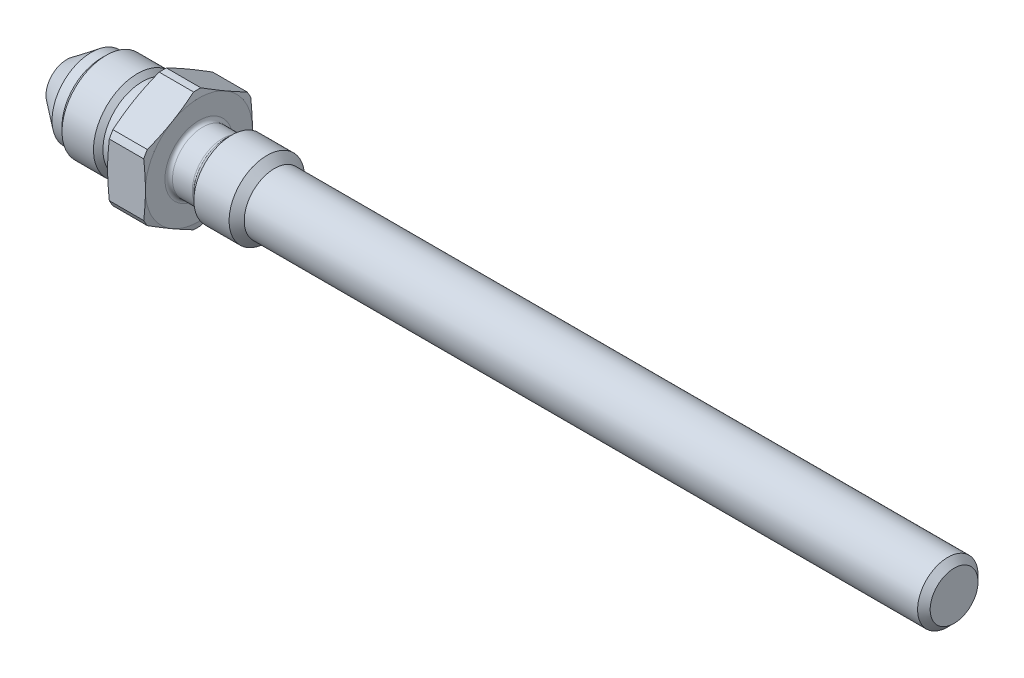
SolidWorks part; units mm, degrees
material "Сплав 3М ОСТ 1.92077-91"
ref_plane "Plane1" through (0, 0, 0) normal (0, 0, 1) x (1, 0, 0)
ref_plane "Plane2" through (0, 0, 0) normal (0, 1, 0) x (1, 0, 0)
ref_plane "Plane3" through (0, 0, 0) normal (1, 0, 0) x (0, 0, -1)
sketch "Эскиз1" plane through (0, 0, 0) normal (0, 0, 1) x (1, 0, 0)
  line L0 (0, 0) -> (-21.5, 0) construction
  line L1 (0, 8.5) -> (0, 4.8)
  line L2 (0, 4.8) -> (4, 4.8)
  line L3 (4, 4.8) -> (5.2, 6)
  line L4 (5.2, 6) -> (10.8, 6)
  line L5 (10.8, 6) -> (12, 4.8)
  line L6 (-6, 8.5) -> (-5.7321, 9.5)
  line L7 (12, 4.8) -> (120, 4.8)
  line L8 (-0.2679, 9.5) -> (-5.7321, 9.5)
  line L9 (-6, 8.5) -> (-6, 6.25)
  line L10 (-6, 6.25) -> (-9, 6.25)
  line L11 (-9, 6.25) -> (-9.75, 7)
  line L12 (-9.75, 7) -> (-14.75, 7)
  line L13 (-14.75, 7) -> (-15.5, 6.25)
  line L14 (-15.5, 6.25) -> (-17.0852, 6.25)
  line L15 (-17.0852, 6.25) -> (-21, 3.3)
  line L16 (-21, 3.3) -> (-21, 3)
  line L17 (-21, 3) -> (114, 3)
  line L18 (120, 0) -> (120, 4.8)
  line L19 (0, 8.5) -> (-0.2679, 9.5)
  line L20 (114, 3) -> (115.8026, 0)
  line L21 (115.8026, 0) -> (120, 0)
  dimension "D1" = 14
  dimension "D2" = 45
  dimension "D3" = 12.5
  dimension "D4" = 3
  dimension "D5" = 12.5
  dimension "D6" = 5.5
  dimension "D7" = 37
  dimension "D8" = 6.6
  dimension "D9" = 6
  dimension "D10" = 15
  dimension "D11" = 45
  dimension "D12" = 6
  dimension "D13" = 4
  dimension "D14" = 9.6
  dimension "D15" = 45
  dimension "D16" = 45
  dimension "D17" = 12
  dimension "D18" = 12
  dimension "D19" = 120
  dimension "D20" = 19
  dimension "D21" = 15
  dimension "D22" = 17
  dimension "D23" = 59
  dimension "D24" = 6
revolve "Повернуть1" add sketch "Эскиз1" angle 360 about L0
sketch "Эскиз2" plane through (-6, 0, 0) normal (-1, 0, 0) x (0, 0, 1)
  line L1 (0, 9.815) -> (-8.5, 4.9075)
  line L2 (-8.5, 4.9075) -> (-8.5, -4.9075)
  line L3 (-8.5, -4.9075) -> (0, -9.815)
  line L4 (0, -9.815) -> (8.5, -4.9075)
  line L5 (8.5, -4.9075) -> (8.5, 4.9075)
  line L6 (8.5, 4.9075) -> (0, 9.815)
  circle A0 centre (0, 0) radius 8.5 construction
  dimension "D1" = 17
extrude "Вырез-Вытянуть1" cut sketch "Эскиз2" against normal through all flip side to cut
sketch "Sketch4" [suppressed] plane through (115, 1.5115, 1.6693) normal (1, 0, 0) x (0, 0, -1)
  line L0 (1.6693, -1.5115) -> (1.6693, 0.5985) construction
  line L1 (1.6693, -1.5115) -> (6.7793, -1.5115) construction
  point P0 (1.6693, -1.5115)
  point P3 (6.7793, -1.5115)
  dimension "D1" = 5.11
  dimension "D2" = 2.11
  dimension "D3" = 90
ref_plane "Plane4_для_эскиза_отверстия" [suppressed] through (115, 0, 0) normal (0, 1, 0) x (-1, 0, 0)
ref_plane "Plane5_начало_резьбы" [suppressed] through (115, 0, 0) normal (-1, 0, 0) x (0, 1, 0)
sketch "Sketch2" [suppressed] plane through (115, 0, 0) normal (0, 1, 0) x (0, 0, 1)
  line L0 (0, 0) -> (0, -16.4571)
  line L1 (-3.9, 0) -> (-3.384, -0.8938)
  line L2 (3.384, -0.8938) -> (3.9, 0) construction
  line L3 (-3.25, -1.3938) -> (-3.25, -3)
  line L4 (-3.25, -3) -> (-2.475, -3.775)
  line L5 (-2.475, -3.775) -> (-2.475, -10)
  line L6 (-2.425, -15) -> (0, -16.4571)
  line L7 (-3.9, 0) -> (0, 0)
  line L8 (0, 0) -> (0, 3.9197) construction
  line L9 (-2.475, -10) -> (-2.425, -10)
  line L11 (3.25, -1.3938) -> (3.25, -3) construction
  line L12 (-2.425, -10) -> (-2.425, -15)
  line L13 (3.25, -3) -> (2.475, -3.775) construction
  line L14 (0, -16.4571) -> (2.425, -15) construction
  arc A0 (-3.384, -0.8938) -> (-3.25, -1.3938) centre (-4.25, -1.3938) cw
  arc A1 (3.25, -1.3938) -> (3.384, -0.8938) centre (4.25, -1.3938) cw construction
  point P2 (-3, -10)
  point P19 (-3.9, 0)
  dimension "D9" = 1
  dimension "D10" = 1
  dimension "D1_уплотнение" = 6.5
  dimension "D2_фаска" = 7.8
  dimension "D3_под_резьбу" = 4.95
  dimension "D4_глубина_сверления" = 15
  dimension "D5" = 3
  dimension "D6" = 60
  dimension "D7" = 90
  dimension "D8" = 118
  dimension "D11" = 0.05
  dimension "D1_диаметр" = 6
  dimension "D2_глубина_резьбы" = 10
revolve "Cut-Revolve1" [suppressed] cut sketch "Sketch2" angle 360 about L8
cosmetic thread "Условное изображение резьбы1" [suppressed] parameters "D1_диаметр"=6
other "Отв_ГОСТ_19529-74 - <1>" [suppressed]
chamfer "Фаска1" distance 1 angle 45 1 edges at (120, 0, -4.8)
fillet "Скругление1" radius 0.6 2 edges at (4, 0, -4.8) (0, 0, -4.8)
